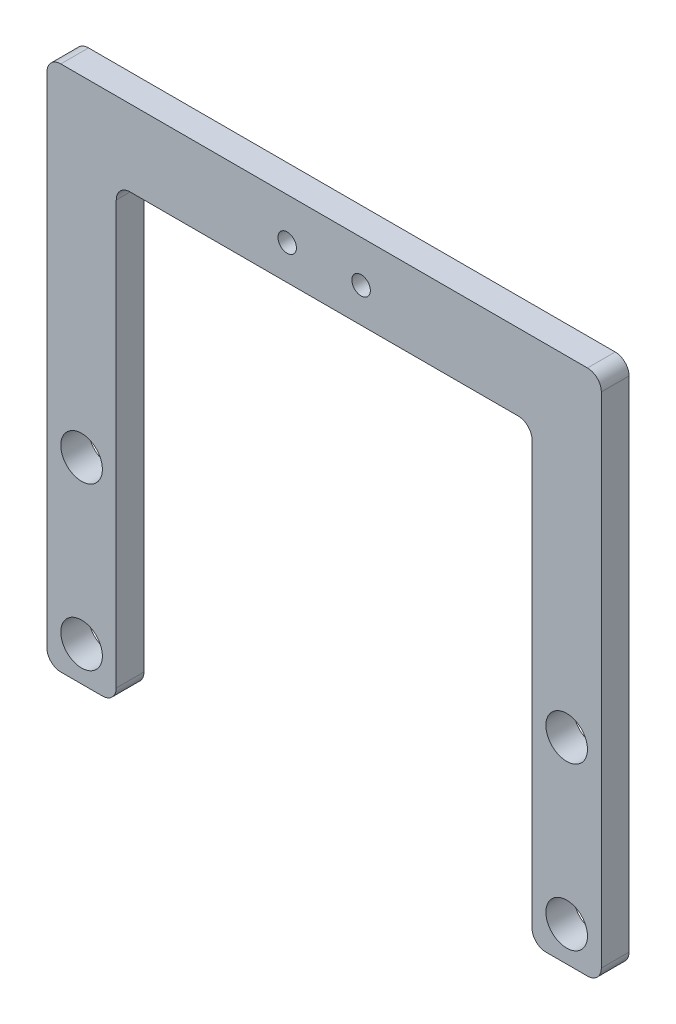
SolidWorks part; units mm, degrees
ref_plane "Front Plane" through (0, 0, 0) normal (0, 0, 1) x (1, 0, 0)
ref_plane "Top Plane" through (0, 0, 0) normal (0, 1, 0) x (1, 0, 0)
ref_plane "Right Plane" through (0, 0, 0) normal (1, 0, 0) x (0, 0, -1)
sketch "Sketch1" plane through (0, 0, 0) normal (0, 0, 1) x (1, 0, 0)
  line L19 (-45, -39.5) -> (-45, 52)
  line L20 (45, -39.5) -> (45, 52)
  line L21 (-57, -42.5) -> (-48, -42.5)
  line L26 (48, -42.5) -> (57, -42.5)
  line L28 (-42, 55) -> (42, 55)
  line L29 (-60, -39.5) -> (-60, 68.5)
  line L30 (-57, 71.5) -> (57, 71.5)
  line L31 (60, 68.5) -> (60, -39.5)
  circle A11 centre (8, 62.5) radius 2
  circle A12 centre (-8, 62.5) radius 2
  circle A13 centre (-52.5, -35) radius 4.5
  circle A14 centre (52.5, -35) radius 4.5
  circle A15 centre (-52.5, 0) radius 4.5
  circle A16 centre (52.5, 0) radius 4.5
  arc A17 (-57, -42.5) -> (-60, -39.5) centre (-57, -39.5) cw
  arc A18 (-45, -39.5) -> (-48, -42.5) centre (-48, -39.5) cw
  arc A19 (48, -42.5) -> (45, -39.5) centre (48, -39.5) cw
  arc A20 (60, -39.5) -> (57, -42.5) centre (57, -39.5) cw
  arc A21 (60, 68.5) -> (57, 71.5) centre (57, 68.5) ccw
  arc A22 (45, 52) -> (42, 55) centre (42, 52) ccw
  arc A23 (-42, 55) -> (-45, 52) centre (-42, 52) ccw
  arc A24 (-57, 71.5) -> (-60, 68.5) centre (-57, 68.5) ccw
  point P15 (-60, -42.5)
  point P22 (45, -42.5)
  point P38 (-60, 71.5)
  dimension "D3" = 3
  dimension "D1" = 114
  dimension "D8" = 8
  dimension "D22" = 4
  dimension "D25" = 4
  dimension "D24" = 8
extrude "Boss-Extrude1" add sketch "Sketch1" along normal blind 6
